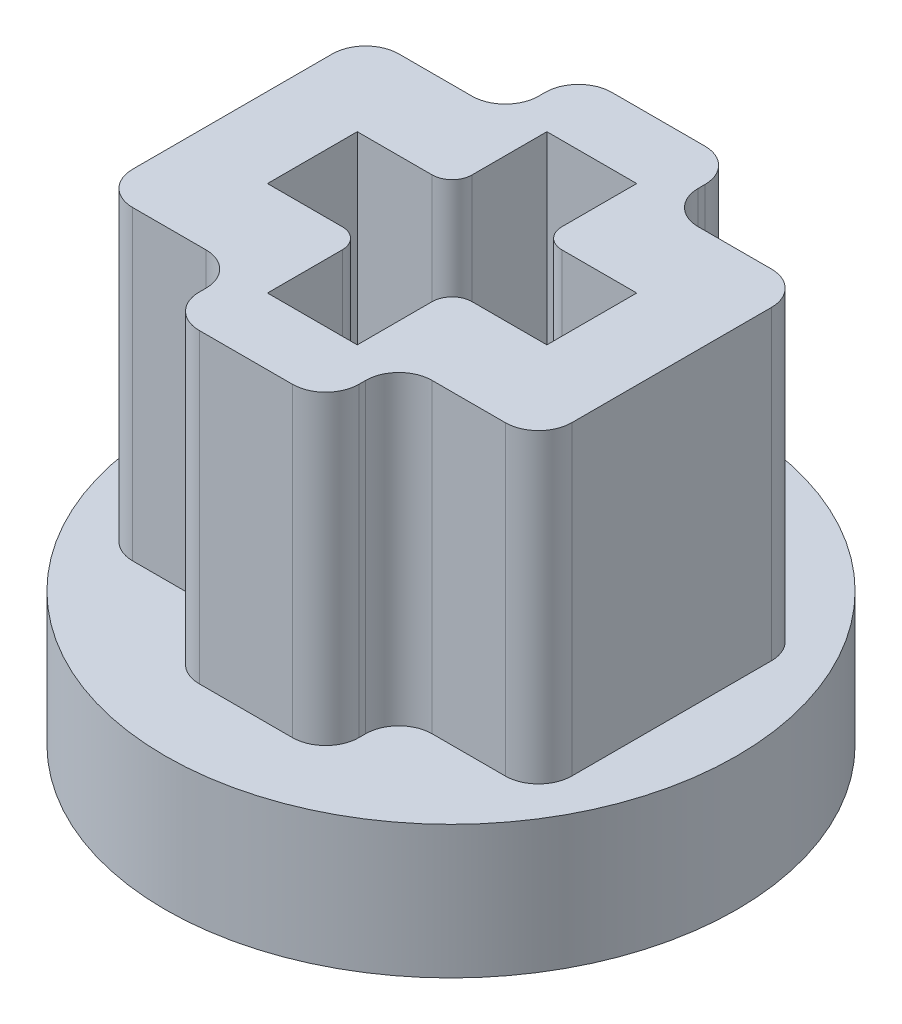
SolidWorks part; units mm, degrees
ref_plane "Front Plane" through (0, 0, 0) normal (0, 0, 1) x (1, 0, 0)
ref_plane "Top Plane" through (0, 0, 0) normal (0, 1, 0) x (1, 0, 0)
ref_plane "Right Plane" through (0, 0, 0) normal (1, 0, 0) x (0, 0, -1)
sketch "Sketch1" plane through (0, 0, 0) normal (0, 1, 0) x (1, 0, 0)
  line L0 (17, 0) -> (-17, 0) construction
  line L1 (17, -12) -> (-17, -12)
  line L2 (17, 12) -> (-17, 12)
  arc A1 (17, -12) -> (17, 12) centre (17, 0) ccw
  arc A2 (-17, 12) -> (-17, -12) centre (-17, 0) ccw
  point P5 (0, 0)
  point P10 (-29, 0)
  point P11 (29, 0)
  dimension "D2" = 12
  dimension "D3" = 58
extrude "button top" add sketch "Sketch1" along normal blind 1.8
sketch "Sketch2" plane through (0, 1.8, 0) normal (0, 1, 0) x (1, 0, 0)
  line L0 (-17, 0) -> (17, 0) construction
  line L1 (-17, 12) -> (17, 12)
  line L2 (-17, -12) -> (17, -12)
  line L3 (-17, 0) -> (17, 0) construction
  line L4 (-17, 10.2) -> (17, 10.2)
  line L5 (-17, -10.2) -> (17, -10.2)
  arc A2 (-17, 12) -> (-17, -12) centre (-17, 0) ccw
  arc A6 (17, -12) -> (17, 12) centre (17, 0) ccw
  arc A7 (17, -12) -> (17, 12) centre (17, 0) ccw construction
  arc A8 (-17, 10.2) -> (-17, -10.2) centre (-17, 0) ccw
  arc A9 (17, -10.2) -> (17, 10.2) centre (17, 0) ccw
  point P2 (0, 0)
  point P15 (0, 0)
  dimension "D1" = 1.8
extrude "button walls" add sketch "Sketch2" along normal blind 4.8
sketch "Sketch5" plane through (0, 1.8, 0) normal (0, 1, 0) x (1, 0, 0)
  line L0 (-12, 0) -> (12, 0) construction
  line L1 (-12, 5) -> (12, 5)
  line L2 (-12, -5) -> (12, -5)
  arc A0 (-12, 5) -> (-12, -5) centre (-12, 0) ccw
  arc A1 (12, -5) -> (12, 5) centre (12, 0) ccw
  point P3 (0, 0)
  dimension "D1" = 5
  dimension "D2" = 24
extrude "offset" add sketch "Sketch5" along normal blind 0.2
sketch "Sketch3" plane through (0, 1.8, 0) normal (0, 1, 0) x (1, 0, 0)
  line L0 (0, -2.1) -> (0, 2.1) construction
  line L1 (-2.1, 0) -> (2.1, 0) construction
  line L2 (-0.675, 0.975) -> (-0.675, 2.1)
  line L3 (-0.675, -2.1) -> (0.675, -2.1)
  line L4 (-0.675, -2.1) -> (-0.675, -0.975)
  line L5 (-0.675, 2.1) -> (0.675, 2.1)
  line L6 (0.675, -2.1) -> (0.675, -0.975)
  line L7 (-0.675, -2.1) -> (0.675, 2.1) construction
  line L8 (-0.675, 2.1) -> (0.675, -2.1) construction
  line L9 (-2.1, -0.675) -> (-0.975, -0.675)
  line L10 (-2.1, -0.675) -> (-2.1, 0.675)
  line L11 (-2.1, 0.675) -> (-0.975, 0.675)
  line L12 (2.1, -0.675) -> (2.1, 0.675)
  line L13 (-2.1, -0.675) -> (2.1, 0.675) construction
  line L14 (-2.1, 0.675) -> (2.1, -0.675) construction
  line L15 (0.975, 0.675) -> (2.1, 0.675)
  line L16 (0.675, 0.975) -> (0.675, 2.1)
  line L17 (0.975, -0.675) -> (2.1, -0.675)
  line L55 (-3.6, -2.6) -> (3.6, -2.6)
  line L56 (-3.6, -2.6) -> (-3.6, 2.6)
  line L57 (-3.6, 2.6) -> (3.6, 2.6)
  line L58 (3.6, -2.6) -> (3.6, 2.6)
  line L59 (-3.6, -2.6) -> (3.6, 2.6) construction
  line L60 (-3.6, 2.6) -> (3.6, -2.6) construction
  line L64 (15.238, -1.5) -> (15.238, 1.5)
  line L65 (12.638, -3.1) -> (11.238, -3.1)
  line L66 (14.038, -0.675) -> (14.038, 0.675)
  line L67 (13.138, 3.1) -> (10.738, -3.1) construction
  line L68 (13.138, -3.1) -> (10.738, 3.1) construction
  line L69 (15.238, 2) -> (8.638, -2) construction
  line L70 (-13.138, 2.5) -> (-13.138, 2.6)
  line L71 (-14.738, -2) -> (-13.638, -2)
  line L72 (-12.613, 0.975) -> (-12.613, 2.1)
  line L73 (-12.613, -2.1) -> (-11.263, -2.1)
  line L74 (-12.613, -2.1) -> (-12.613, -0.975)
  line L75 (-12.613, 2.1) -> (-11.263, 2.1)
  line L76 (-11.263, -2.1) -> (-11.263, -0.975)
  line L77 (-14.038, -0.675) -> (-12.913, -0.675)
  line L78 (-14.038, -0.675) -> (-14.038, 0.675)
  line L79 (-14.038, 0.675) -> (-12.913, 0.675)
  line L80 (-9.838, -0.675) -> (-9.838, 0.675)
  line L81 (-10.963, 0.675) -> (-9.838, 0.675)
  line L82 (-11.263, 0.975) -> (-11.263, 2.1)
  line L83 (-10.963, -0.675) -> (-9.838, -0.675)
  line L88 (-11.938, -2.1) -> (-11.938, 2.1) construction
  line L89 (-14.038, 0) -> (-9.838, 0) construction
  line L90 (-12.613, -2.1) -> (-11.263, 2.1) construction
  line L91 (-12.613, 2.1) -> (-11.263, -2.1) construction
  line L92 (-14.038, -0.675) -> (-9.838, 0.675) construction
  line L93 (-14.038, 0.675) -> (-9.838, -0.675) construction
  line L94 (-15.238, -1.5) -> (-15.238, 1.5)
  line L95 (-14.738, 2) -> (-13.638, 2)
  line L96 (15.238, -2) -> (8.638, 2) construction
  line L97 (14.038, 0.675) -> (9.838, -0.675) construction
  line L98 (14.038, -0.675) -> (9.838, 0.675) construction
  line L99 (12.613, 2.1) -> (11.263, -2.1) construction
  line L100 (12.613, -2.1) -> (11.263, 2.1) construction
  line L101 (14.038, 0) -> (9.838, 0) construction
  line L102 (-15.538, -2.6) -> (-8.338, -2.6) [skipped]
  line L103 (-15.538, 2.6) -> (-8.338, 2.6) [skipped]
  line L104 (-8.338, -2.6) -> (-8.338, 2.6) [skipped]
  line L105 (-15.538, -2.6) -> (-8.338, 2.6) construction
  line L106 (-15.538, 2.6) -> (-8.338, -2.6) construction
  line L107 (-15.538, -2.6) -> (-15.538, 2.6) [skipped]
  line L108 (-8.638, -1.5) -> (-8.638, 1.5)
  line L109 (-15.238, -2) -> (-8.638, 2) construction
  line L110 (-15.238, 2) -> (-8.638, -2) construction
  line L111 (-12.638, -3.1) -> (-11.238, -3.1)
  line L112 (-13.138, -2.6) -> (-13.138, -2.5)
  line L113 (-12.638, 3.1) -> (-11.238, 3.1)
  line L114 (-10.738, -2.6) -> (-10.738, -2.5)
  line L115 (-13.138, -3.1) -> (-10.738, 3.1) construction
  line L116 (-13.138, 3.1) -> (-10.738, -3.1) construction
  line L117 (-10.238, 2) -> (-9.138, 2)
  line L118 (-10.738, 2.5) -> (-10.738, 2.6)
  line L119 (-10.238, -2) -> (-9.138, -2)
  line L120 (11.938, -2.1) -> (11.938, 2.1) construction
  line L121 (10.238, -2) -> (9.138, -2)
  line L122 (10.738, -2.6) -> (10.738, -2.5)
  line L123 (13.138, -2.6) -> (13.138, -2.5)
  line L124 (14.738, 2) -> (13.638, 2)
  line L125 (10.963, -0.675) -> (9.838, -0.675)
  line L126 (11.263, 0.975) -> (11.263, 2.1)
  line L127 (10.963, 0.675) -> (9.838, 0.675)
  line L128 (9.838, -0.675) -> (9.838, 0.675)
  line L129 (14.038, 0.675) -> (12.913, 0.675)
  line L130 (14.038, -0.675) -> (12.913, -0.675)
  line L131 (11.263, -2.1) -> (11.263, -0.975)
  line L132 (12.613, 2.1) -> (11.263, 2.1)
  line L133 (12.613, -2.1) -> (12.613, -0.975)
  line L134 (12.613, -2.1) -> (11.263, -2.1)
  line L135 (12.613, 0.975) -> (12.613, 2.1)
  line L136 (14.738, -2) -> (13.638, -2)
  line L137 (13.138, 2.5) -> (13.138, 2.6)
  line L138 (10.738, 2.5) -> (10.738, 2.6)
  line L139 (10.238, 2) -> (9.138, 2)
  line L140 (8.638, -1.5) -> (8.638, 1.5)
  line L141 (12.638, 3.1) -> (11.238, 3.1)
  circle A0 centre (0, 0) radius 3
  arc A1 (-0.675, -0.975) -> (-0.975, -0.675) centre (-0.975, -0.975) ccw
  arc A2 (0.675, -0.975) -> (0.975, -0.675) centre (0.975, -0.975) cw
  arc A3 (0.975, 0.675) -> (0.675, 0.975) centre (0.975, 0.975) cw
  arc A4 (-0.675, 0.975) -> (-0.975, 0.675) centre (-0.975, 0.975) cw
  arc A11 (-12.613, -0.975) -> (-12.913, -0.675) centre (-12.913, -0.975) ccw
  arc A12 (-11.263, -0.975) -> (-10.963, -0.675) centre (-10.963, -0.975) cw
  arc A13 (-10.963, 0.675) -> (-11.263, 0.975) centre (-10.963, 0.975) cw
  arc A14 (-12.613, 0.975) -> (-12.913, 0.675) centre (-12.913, 0.975) cw
  arc A15 (10.738, -2.5) -> (10.238, -2) centre (10.238, -2.5) ccw
  circle A16 centre (-11.938, 0) radius 3 [skipped]
  arc A18 (-13.138, -2.5) -> (-13.638, -2) centre (-13.638, -2.5) ccw
  arc A19 (-10.738, -2.5) -> (-10.238, -2) centre (-10.238, -2.5) cw
  arc A20 (-10.238, 2) -> (-10.738, 2.5) centre (-10.238, 2.5) cw
  arc A21 (-13.138, 2.5) -> (-13.638, 2) centre (-13.638, 2.5) cw
  arc A22 (13.138, -2.5) -> (13.638, -2) centre (13.638, -2.5) cw
  arc A23 (12.613, 0.975) -> (12.913, 0.675) centre (12.913, 0.975) ccw
  arc A24 (10.963, 0.675) -> (11.263, 0.975) centre (10.963, 0.975) ccw
  arc A25 (11.263, -0.975) -> (10.963, -0.675) centre (10.963, -0.975) ccw
  arc A26 (12.613, -0.975) -> (12.913, -0.675) centre (12.913, -0.975) cw
  arc A27 (13.138, 2.5) -> (13.638, 2) centre (13.638, 2.5) ccw
  arc A28 (10.238, 2) -> (10.738, 2.5) centre (10.238, 2.5) ccw
  arc A29 (15.238, -1.5) -> (14.738, -2) centre (14.738, -1.5) cw
  arc A30 (12.638, -3.1) -> (13.138, -2.6) centre (12.638, -2.6) ccw
  arc A31 (11.238, -3.1) -> (10.738, -2.6) centre (11.238, -2.6) cw
  arc A32 (8.638, -1.5) -> (9.138, -2) centre (9.138, -1.5) ccw
  arc A33 (8.638, 1.5) -> (9.138, 2) centre (9.138, 1.5) cw
  arc A34 (11.238, 3.1) -> (10.738, 2.6) centre (11.238, 2.6) ccw
  arc A35 (12.638, 3.1) -> (13.138, 2.6) centre (12.638, 2.6) cw
  arc A36 (15.238, 1.5) -> (14.738, 2) centre (14.738, 1.5) ccw
  arc A37 (-9.138, 2) -> (-8.638, 1.5) centre (-9.138, 1.5) cw
  arc A38 (-9.138, -2) -> (-8.638, -1.5) centre (-9.138, -1.5) ccw
  arc A39 (-11.238, -3.1) -> (-10.738, -2.6) centre (-11.238, -2.6) ccw
  arc A40 (-12.638, -3.1) -> (-13.138, -2.6) centre (-12.638, -2.6) cw
  arc A41 (-14.738, -2) -> (-15.238, -1.5) centre (-14.738, -1.5) cw
  arc A42 (-15.238, 1.5) -> (-14.738, 2) centre (-14.738, 1.5) cw
  arc A43 (-13.138, 2.6) -> (-12.638, 3.1) centre (-12.638, 2.6) cw
  arc A44 (-11.238, 3.1) -> (-10.738, 2.6) centre (-11.238, 2.6) cw
  point P6 (0, 0)
  point P9 (0, 0)
  point P22 (2.1, 0)
  point P23 (0, 0)
  point P24 (0, 2.1)
  point P29 (0.675, -0.675)
  point P32 (0.675, 0.675)
  point P38 (-11.938, 0)
  point P76 (-11.938, 0)
  point P79 (-11.938, 0)
  point P101 (-11.938, 0)
  point P136 (-11.938, 3.1)
  point P141 (-10.738, -2)
  point P144 (-10.738, 2)
  dimension "D1" = 6
  dimension "D4" = 0.3
  dimension "D16" = 0.5
  dimension "D5" = 0.5
  dimension "D2" = 4.2
  dimension "D3" = 1.35
  dimension "D7" = 11.938
  dimension "D9" = 7.2
  dimension "D10" = 5.2
  dimension "D12" = 4
  dimension "D13" = 6.6
  dimension "D14" = 2.4
  dimension "D15" = 6.2
  dimension "D6" = 2
extrude "stem housing" add sketch "Sketch3" along normal blind 4.6 from surface
sketch "Sketch4" plane through (0, 1.8, 0) normal (0, 1, 0) x (1, 0, 0)
  line L0 (0, 3) -> (0, 10.2) construction
  line L1 (-0.8, 3) -> (-0.8, 10.2)
  line L2 (0.8, 3) -> (0.8, 10.2)
  line L3 (0, -3.63) -> (0, 3.63) construction
  line L6 (-17, 0) -> (-27.2, 0) construction
  line L18 (17, 0) -> (27.2, 0) construction
  line L19 (17, -0.8) -> (27.2, -0.8)
  line L20 (17, 0.8) -> (27.2, 0.8)
  line L21 (12, 3.1) -> (12, 10.2) construction
  line L22 (11.2, 3.1) -> (11.2, 10.2)
  line L23 (12.8, 3.1) -> (12.8, 10.2)
  line L24 (-12, 3.1) -> (-12, 10.2) construction
  line L25 (-12.8, 3.1) -> (-12.8, 10.2)
  line L26 (-11.2, 3.1) -> (-11.2, 10.2)
  line L27 (-17, -0.8) -> (-27.2, -0.8)
  line L28 (-17, 0.8) -> (-27.2, 0.8)
  line L29 (-3.63, 0) -> (3.63, 0) construction
  line L32 (11.238, 3.1) -> (12.638, 3.1) construction
  line L35 (0, -3) -> (0, -10.2) construction
  line L36 (-0.8, -3) -> (-0.8, -10.2)
  line L37 (0.8, -3) -> (0.8, -10.2)
  line L38 (12, -3.1) -> (12, -10.2) construction
  line L39 (11.2, -3.1) -> (11.2, -10.2)
  line L40 (12.8, -3.1) -> (12.8, -10.2)
  line L41 (-12, -3.1) -> (-12, -10.2) construction
  line L42 (-12.8, -3.1) -> (-12.8, -10.2)
  line L43 (-11.2, -3.1) -> (-11.2, -10.2)
  line L44 (17, 10.2) -> (-17, 10.2) construction
  line L45 (17, 10.2) -> (-17, 10.2) construction
  line L46 (-17, -10.2) -> (17, -10.2) construction
  line L47 (-11.238, 3.1) -> (-12.638, 3.1) construction
  arc A1 (-12, 5) -> (-12, -5) centre (-12, 0) ccw construction
  arc A3 (-0.8, 3) -> (0.8, 3) centre (0, 3) ccw
  arc A4 (0.8, 10.2) -> (-0.8, 10.2) centre (0, 10.2) ccw
  arc A17 (17, -0.8) -> (17, 0.8) centre (17, 0) cw
  arc A18 (27.2, 0.8) -> (27.2, -0.8) centre (27.2, 0) cw
  arc A19 (11.2, 3.1) -> (12.8, 3.1) centre (12, 3.1) ccw
  arc A20 (12.8, 10.2) -> (11.2, 10.2) centre (12, 10.2) ccw
  arc A21 (-12.8, 3.1) -> (-11.2, 3.1) centre (-12, 3.1) ccw
  arc A22 (-11.2, 10.2) -> (-12.8, 10.2) centre (-12, 10.2) ccw
  arc A25 (-17, 10.2) -> (-17, -10.2) centre (-17, 0) ccw construction
  arc A26 (-17, -0.8) -> (-17, 0.8) centre (-17, 0) ccw
  arc A27 (-27.2, 0.8) -> (-27.2, -0.8) centre (-27.2, 0) ccw
  arc A28 (1.4967, 2.6) -> (-1.4967, 2.6) centre (0, 0) ccw construction
  arc A35 (-0.8, -3) -> (0.8, -3) centre (0, -3) cw
  arc A36 (0.8, -10.2) -> (-0.8, -10.2) centre (0, -10.2) cw
  arc A37 (11.2, -3.1) -> (12.8, -3.1) centre (12, -3.1) cw
  arc A38 (12.8, -10.2) -> (11.2, -10.2) centre (12, -10.2) cw
  arc A39 (-12.8, -3.1) -> (-11.2, -3.1) centre (-12, -3.1) cw
  arc A40 (-11.2, -10.2) -> (-12.8, -10.2) centre (-12, -10.2) cw
  point P2 (-11.938, 3.1)
  point P4 (12, 3.1)
  point P7 (-11.238, 3.4222)
  point P9 (0, 6.6)
  point P19 (-12, 3.1)
  point P33 (22.1, 0)
  point P40 (12, 6.65)
  point P47 (-12, 6.65)
  point P55 (0, -6.6)
  point P59 (-22.1, 0)
  point P69 (12, -6.65)
  point P76 (-12, -6.65)
  dimension "D1" = 1.6
  dimension "D4" = 12
  dimension "D5" = 12
extrude "spokes" add sketch "Sketch4" along normal up to surface (0.2 mm away) up to face at (0, 2, 0)
fillet "Fillet1" [suppressed] radius 1.5
chamfer "Chamfer1" distance 1.5 angle 45 4 edges at (0, 6.6, 10.2) (27.2, 6.6, 0) (-27.2, 6.6, 0) (0, 6.6, -10.2)
sketch "Sketch6" plane through (0, 0, 0) normal (0, 0, 1) x (1, 0, 0)
  line L0 (-28.2615, 0) -> (-28.4615, 0.2)
  line L1 (-17, 0) -> (17, 0) construction
  line L2 (-29, 6.6) -> (-29, 0) construction
  line L3 (-29, 1.5) -> (-29, 0)
  line L7 (-29, 0) -> (-28.2615, 0)
  arc A0 (-28.4615, 0.2) -> (-29, 1.5) centre (-27.1615, 1.5) cw
  dimension "D1" = 0.2
  dimension "D2" = 1.5
  dimension "D3" = 45
sketch "Sketch10" plane through (0, 0, 0) normal (0, -1, 0) x (1, 0, 0)
  line L0 (-17, 12) -> (17, 12)
  line L1 (17, -12) -> (-17, -12)
  arc A0 (-17, -12) -> (-17, 12) centre (-17, 0) cw
  arc A1 (17, 12) -> (17, -12) centre (17, 0) cw
sweep "Cut-Sweep1" cut profiles "Sketch6" path "Sketch10"
sketch "Sketch11" plane through (0, 2, 0) normal (0, 1, 0) x (1, 0, 0)
  circle A0 centre (-11.9543, 0) radius 4.2951
  circle A1 centre (-11.9543, 0) radius 47.7768
extrude "Cut-Extrude1" cut sketch "Sketch11" against normal blind 10 and the other way blind 10
